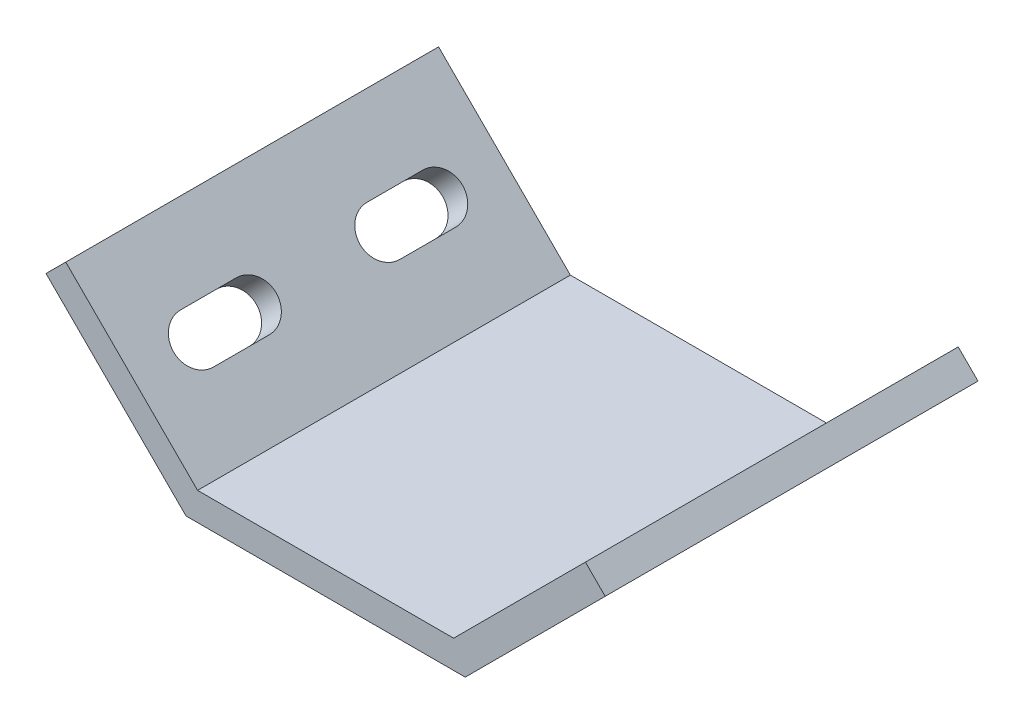
SolidWorks part; units mm, degrees
material "Алюминий"
ref_plane "Спереди" through (0, 0, 0) normal (0, 0, 1) x (1, 0, 0)
ref_plane "Сверху" through (0, 0, 0) normal (0, 1, 0) x (1, 0, 0)
ref_plane "Справа" through (0, 0, 0) normal (1, 0, 0) x (0, 0, -1)
sketch "Эскиз1" plane through (0, 0, 0) normal (0, 0, 1) x (1, 0, 0)
  line L0 (-13.7365, 0) -> (13.7365, 0)
  line L1 (13.7365, 0) -> (27.8787, 14.1421)
  line L2 (0, 0) -> (0, 29.6898) construction
  line L3 (-13.7365, 0) -> (-27.8787, 14.1421)
  line L4 (13.7365, 0) -> (-0.4056, 14.1421) construction
  line L5 (-0.4056, 14.1421) -> (13.7365, 28.2843) construction
  line L6 (13.7365, 28.2843) -> (27.8787, 14.1421) construction
  line L7 (-27.8787, 14.1421) -> (-13.7365, 28.2843) construction
  line L8 (-13.7365, 28.2843) -> (0.4056, 14.1421) construction
  line L9 (0.4056, 14.1421) -> (-13.7365, 0) construction
  line L10 (-27.8787, 14.1421) -> (-30, 12.0208) construction
  line L11 (27.8787, 14.1421) -> (30, 12.0208) construction
  dimension "D1" = 90
  dimension "D2" = 20
  dimension "D3" = 3
  dimension "D4" = 55.7574
  dimension "D5" = 60
extrude "Вытянуть-Тонкостенный1" add sketch "Эскиз1" along normal blind 20 thin
sketch "Эскиз2" plane through (-6.8683, -6.8683, 0) normal (0.7071, 0.7071, 0) x (0, 0, -1)
  line L0 (-7, 19.7132) -> (-13, 19.7132) construction
  line L1 (-7, 17.2132) -> (-13, 17.2132)
  line L2 (-7, 22.2132) -> (-13, 22.2132)
  line L3 (-10, 19.7132) -> (-10, 9.7132) construction
  line L4 (-20, 9.7132) -> (0, 9.7132) construction
  line L5 (-10, 19.7132) -> (-10, 29.7132) construction
  line L6 (-20, 29.7132) -> (0, 29.7132) construction
  arc A0 (-7, 17.2132) -> (-7, 22.2132) centre (-7, 19.7132) ccw
  arc A1 (-13, 22.2132) -> (-13, 17.2132) centre (-13, 19.7132) ccw
  point P2 (-10, 19.7132)
  dimension "D2" = 11
  dimension "D1" = 5
extrude "Вырез-Вытянуть1" cut sketch "Эскиз2" against normal through all
mirror "Зеркальное отражение1" about plane through (0, 0, 0) normal (1, 0, 0) of "Вырез-Вытянуть1"
mirror "Зеркальное отражение2" about plane through (0, 0, 0) normal (0, 0, -1) of bodies 112
